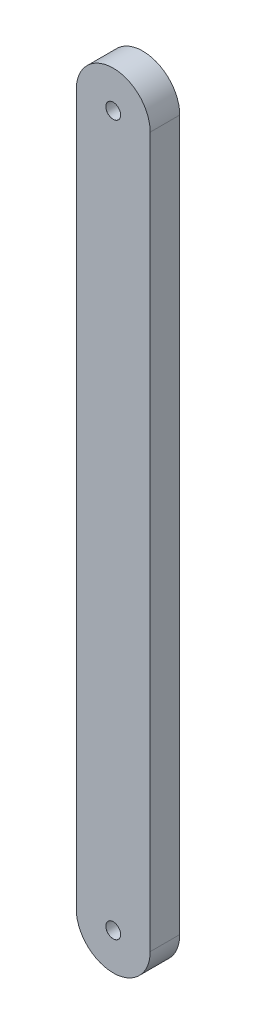
SolidWorks part; units mm, degrees
material "Alloy Steel"
ref_plane "Front Plane" through (0, 0, 0) normal (0, 0, 1) x (1, 0, 0)
ref_plane "Top Plane" through (0, 0, 0) normal (0, 1, 0) x (1, 0, 0)
ref_plane "Right Plane" through (0, 0, 0) normal (1, 0, 0) x (0, 0, -1)
sketch "Sketch1" plane through (0, 0, 0) normal (0, 0, 1) x (1, 0, 0)
  line L0 (0, 0) -> (0, 480)
  line L1 (50, 480) -> (50, 0)
  arc A0 (0, 480) -> (50, 480) centre (25, 480) cw
  arc A1 (50, 0) -> (0, 0) centre (25, 0) cw
  point P7 (0, 240)
  dimension "D1" = 480
  dimension "D2" = 50
extrude "Boss-Extrude1" add sketch "Sketch1" along normal blind 20
hole_wizard "Ø10.0mm Dowel Hole1" positions "Sketch2" profile "Sketch3" hole size "Ø10.0" standard "ANSI Metric" end condition up to next
sketch "Sketch2" plane through (0, 0, 20) normal (0, 0, 1) x (1, 0, 0)
  point P0 (25, 480)
  point P3 (25, 0)
sketch "Sketch3" plane through (25, 480, 20) normal (1, 0, 0) x (0, -1, 0)
  line L0 (0, 0) -> (0, 20)
  line L1 (0, 20) -> (5, 20)
  line L2 (5, 20) -> (5, 0.025)
  line L3 (5, 0.025) -> (5.025, 0)
  line L5 (5.025, 0) -> (0, 0)
  line L6 (-5, 0.025) -> (-5.025, 0) construction
  line L11 (0, -6.35) -> (0, 107.95) construction
  dimension "Thru Hole Dia." = 10
  dimension "Thru Hole Depth" = 20
  dimension "Near C'Sink Dia." = 10.05
  dimension "Near C'Sink Angle" = 90
